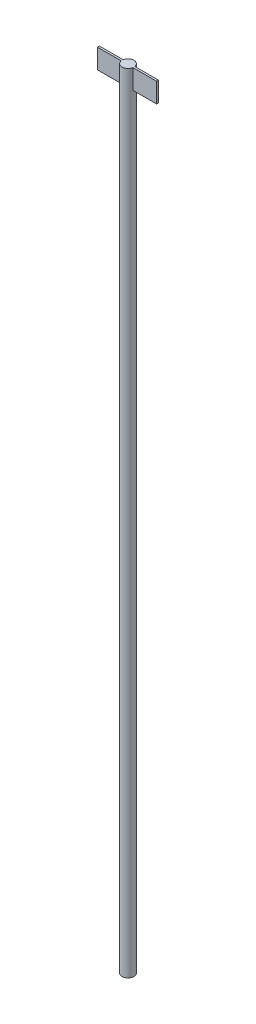
SolidWorks part; units mm, degrees
ref_plane "Front Plane" through (0, 0, 0) normal (0, 0, 1) x (1, 0, 0)
ref_plane "Top Plane" through (0, 0, 0) normal (0, 1, 0) x (1, 0, 0)
ref_plane "Right Plane" through (0, 0, 0) normal (1, 0, 0) x (0, 0, -1)
sketch "Sketch1" plane through (0, 0, 0) normal (0, 1, 0) x (1, 0, 0)
  circle A0 centre (0, 0) radius 1.5
  dimension "D1" = 3
extrude "Boss-Extrude1" add sketch "Sketch1" along normal mid plane 200
sketch "Sketch2" plane through (0, 100, 0) normal (0, 1, 0) x (1, 0, 0)
  line L1 (-7.5, 0.25) -> (7.5, 0.25)
  line L2 (-7.5, 0.25) -> (-7.5, -0.25)
  line L3 (-7.5, -0.25) -> (7.5, -0.25)
  line L4 (7.5, 0.25) -> (7.5, -0.25)
  line L5 (-7.5, 0.25) -> (7.5, -0.25) construction
  line L6 (-7.5, -0.25) -> (7.5, 0.25) construction
  point P0 (0, 0)
  dimension "D1" = 15
  dimension "D2" = 0.5
extrude "Boss-Extrude2" add sketch "Sketch2" against normal blind 5
